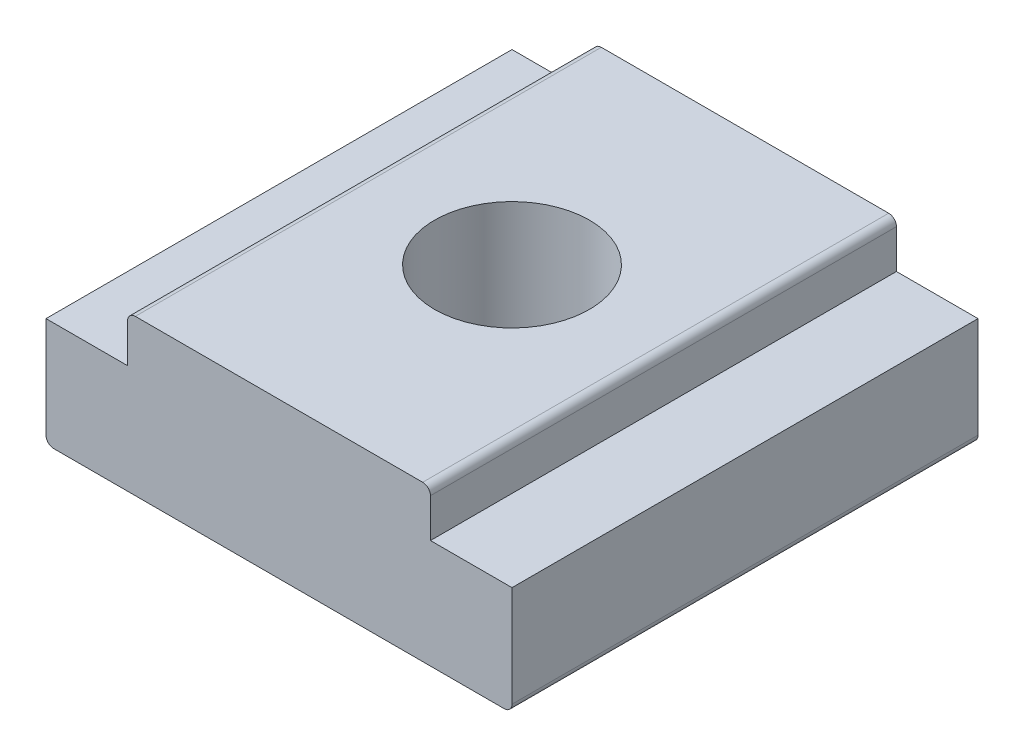
SolidWorks part; units mm, degrees
ref_plane "Front Plane" through (0, 0, 0) normal (0, 0, 1) x (1, 0, 0)
ref_plane "Top Plane" through (0, 0, 0) normal (0, 1, 0) x (1, 0, 0)
ref_plane "Right Plane" through (0, 0, 0) normal (1, 0, 0) x (0, 0, -1)
sketch "Sketch1" plane through (0, 0, 0) normal (0, 0, 1) x (1, 0, 0)
  line L0 (0, 0) -> (0, 15.875) construction
  line L1 (15.4781, 15.875) -> (-15.4781, 15.875)
  line L2 (-15.4781, 15.875) -> (-15.4781, 11.1125)
  line L3 (-15.4781, 11.1125) -> (-23.8125, 11.1125)
  line L4 (-23.8125, 11.1125) -> (-23.8125, 0)
  line L5 (-23.8125, 0) -> (23.8125, 0)
  line L6 (23.8125, 11.1125) -> (23.8125, 0)
  line L7 (15.4781, 11.1125) -> (23.8125, 11.1125)
  line L8 (15.4781, 15.875) -> (15.4781, 11.1125)
  dimension "D1" = 15.875
  dimension "D2" = 23.8125
  dimension "D3" = 11.1125
  dimension "D4" = 15.4781
extrude "Boss-Extrude1" add sketch "Sketch1" along normal mid plane 47.625
sketch "Sketch2" plane through (0, 15.875, 0) normal (0, 1, 0) x (1, 0, 0)
  circle A0 centre (0, 0) radius 7.9121
  dimension "D1" = 15.8242
extrude "Cut-Extrude1" cut sketch "Sketch2" against normal through all
fillet "Fillet1" radius 0.7937 4 edges at (-23.8125, 0, 0) (23.8125, 0, 0) (-15.4781, 15.875, 0) (15.4781, 15.875, 0)
